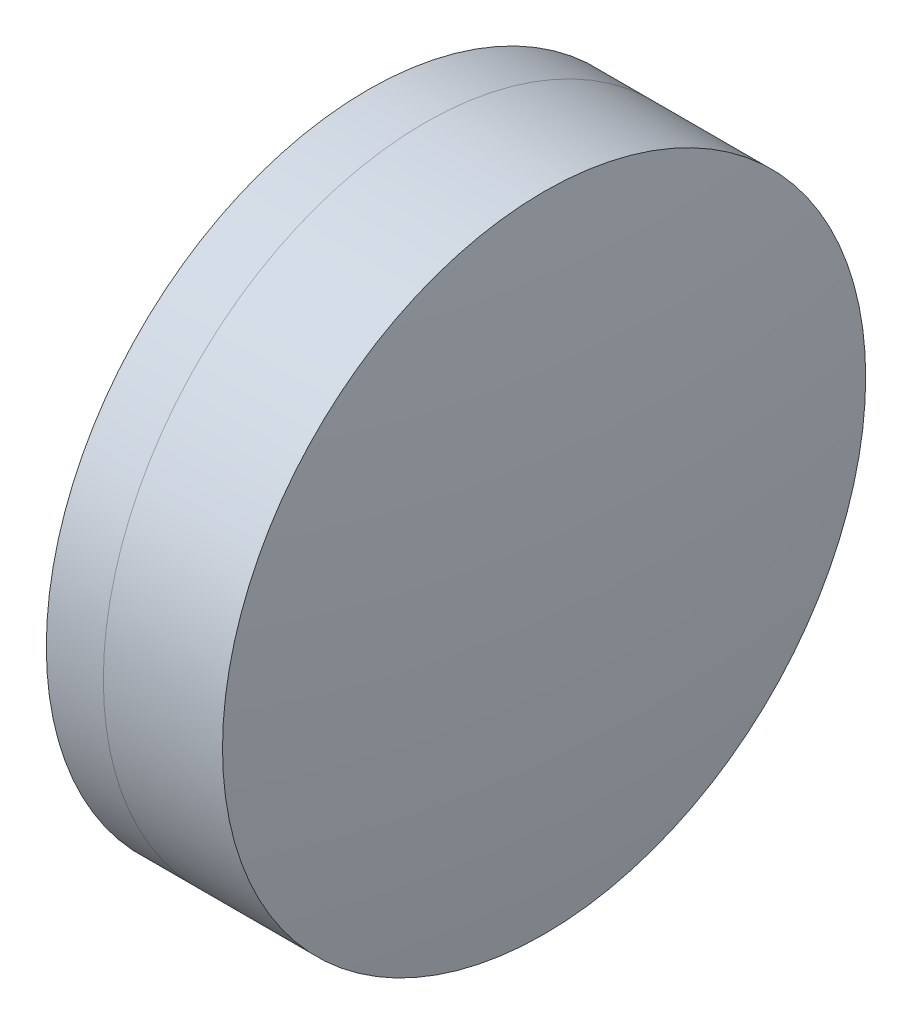
SolidWorks part; units mm, degrees
ref_plane "前视基准面" through (0, 0, 0) normal (0, 0, 1) x (1, 0, 0)
ref_plane "上视基准面" through (0, 0, 0) normal (0, 1, 0) x (1, 0, 0)
ref_plane "右视基准面" through (0, 0, 0) normal (1, 0, 0) x (0, 0, -1)
sketch "草图1" plane through (0, 0, 0) normal (0, 1, 0) x (1, 0, 0)
  line L0 (-9.7026, 0) -> (42.9866, 0) construction
  line L1 (31.1061, -12.5) -> (33.3228, -12.5)
  line L2 (31.1061, 12.5) -> (33.3228, 12.5)
  arc A0 (33.3228, -12.5) -> (33.3228, 12.5) centre (14.8797, 0) ccw
  arc A1 (31.1061, 12.5) -> (31.1061, -12.5) centre (57.1297, 0) ccw
  point P10 (28.2597, 0)
  point P11 (37.1597, 0)
  dimension "D3" = 28.87
  dimension "D4" = 22.28
  dimension "D1" = 12.5
  dimension "D2" = 12.5
  dimension "D5" = 8.9
revolve "旋转1" add sketch "草图1" angle 360 about L0
sketch "草图2" plane through (0, 0, 0) normal (0, 1, 0) x (1, 0, 0)
  line L0 (-0.5519, 0) -> (47.7152, 0) construction
  line L2 (33.3228, 12.5) -> (37.9551, 12.5)
  line L3 (33.3228, -12.5) -> (37.9551, -12.5)
  arc A0 (37.9551, -12.5) -> (37.9551, 12.5) centre (-58.7403, 0) ccw
  arc A1 (33.3228, -12.5) -> (33.3228, 12.5) centre (14.8797, 0) ccw construction
  arc A2 (33.3228, -12.5) -> (33.3228, 12.5) centre (14.8797, 0) ccw
  point P4 (37.1597, 0)
  point P8 (38.7597, 0)
  dimension "D1" = 97.5
  dimension "D2" = 1.6
revolve "旋转3" add sketch "草图2" angle 360 about L0
